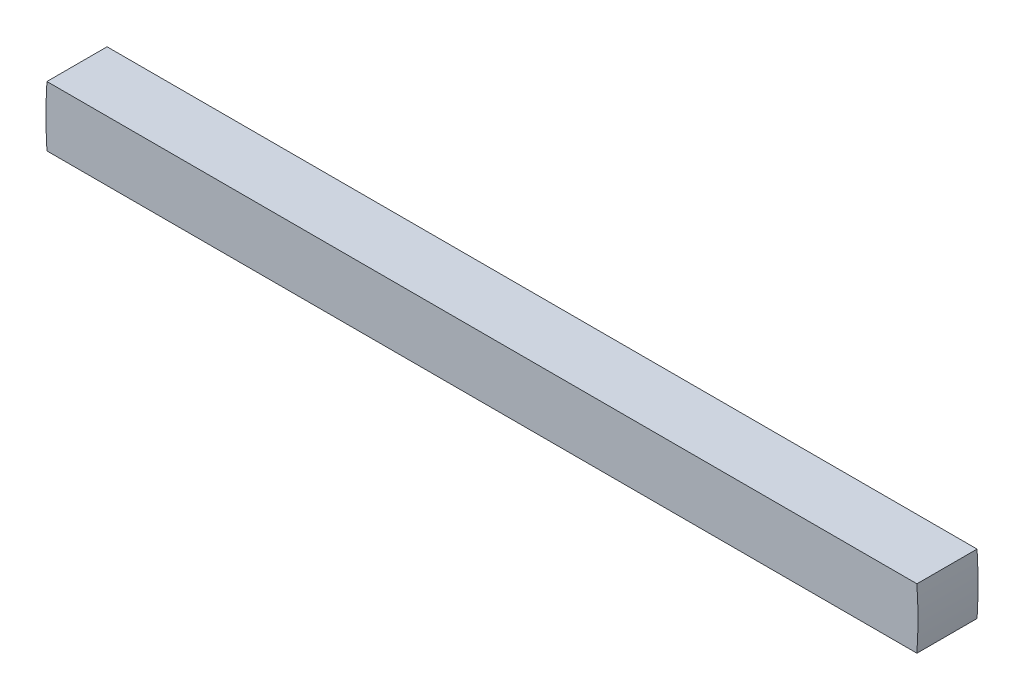
SolidWorks part; units mm, degrees
ref_plane "Front Plane" through (0, 0, 0) normal (0, 0, 1) x (1, 0, 0)
ref_plane "Top Plane" through (0, 0, 0) normal (0, 1, 0) x (1, 0, 0)
ref_plane "Right Plane" through (0, 0, 0) normal (1, 0, 0) x (0, 0, -1)
sketch "Sketch1" plane through (0, 0, 0) normal (0, 0, 1) x (1, 0, 0)
  line L1 (-22.9639, -1.5875) -> (22.9639, -1.5875)
  line L3 (-22.9639, 1.5875) -> (22.9639, 1.5875)
  line L5 (-22.9639, -1.5875) -> (22.9639, 1.5875) construction
  line L6 (-22.9639, 1.5875) -> (22.9639, -1.5875) construction
  circle A0 centre (0, 0) radius 19.8438 construction
  circle A1 centre (0, 0) radius 23.0188 construction
  arc A2 (-22.9639, -1.5875) -> (-22.9639, 1.5875) centre (0, 0) cw
  arc A3 (22.9639, -1.5875) -> (22.9639, 1.5875) centre (0, 0) ccw
  dimension "D1" = 39.6875
  dimension "D3" = 3.175
  dimension "D2" = 3.175
extrude "Boss-Extrude1" add sketch "Sketch1" along normal blind 5.1359
sketch "Sketch2" plane through (0, 0, 5.1359) normal (0, 0, 1) x (1, 0, 0)
  circle A0 centre (0, 0) radius 19.8438
  dimension "D1" = 39.6875
extrude "Cut-Extrude1" cut sketch "Sketch2" against normal blind 1.9609
sketch "Sketch4" plane through (0, 1.5875, 0) normal (0, 1, 0) x (1, 0, 0)
  line L0 (19.7801, -3.175) -> (-19.7801, -3.175) construction
  line L1 (-26.6365, -3.175) -> (26.5051, -3.175)
  line L2 (-26.6365, -3.175) -> (-26.6365, -13.2397)
  line L3 (-26.6365, -13.2397) -> (26.5051, -13.2397)
  line L4 (26.5051, -3.175) -> (26.5051, -13.2397)
extrude "Cut-Extrude3" cut sketch "Sketch4" against normal through all
